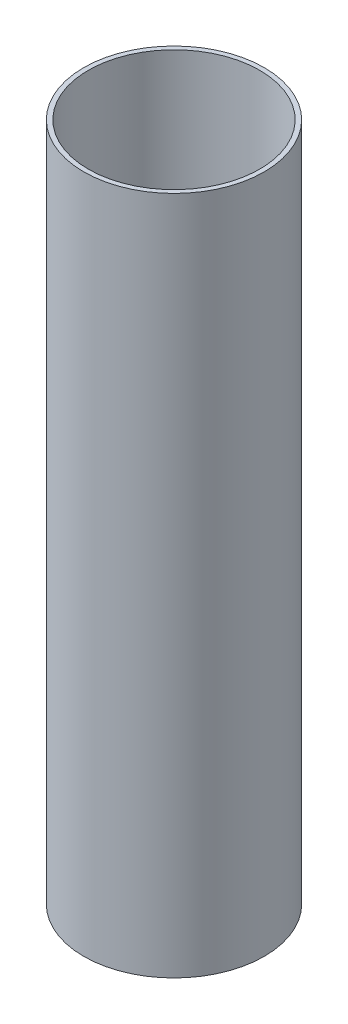
SolidWorks part; units mm, degrees
material "PVC Rigid"
ref_plane "Front Plane" through (0, 0, 0) normal (0, 0, 1) x (1, 0, 0)
ref_plane "Top Plane" through (0, 0, 0) normal (0, 1, 0) x (1, 0, 0)
ref_plane "Right Plane" through (0, 0, 0) normal (1, 0, 0) x (0, 0, -1)
sketch "Sketch1" plane through (0, 0, 0) normal (0, 1, 0) x (1, 0, 0)
  circle A0 centre (0, 0) radius 93.6625
  circle A1 centre (0, 0) radius 88.9
  dimension "D1" = 187.325
  dimension "D2" = 177.8
extrude "Boss-Extrude1" add sketch "Sketch1" along normal mid plane 704.85
